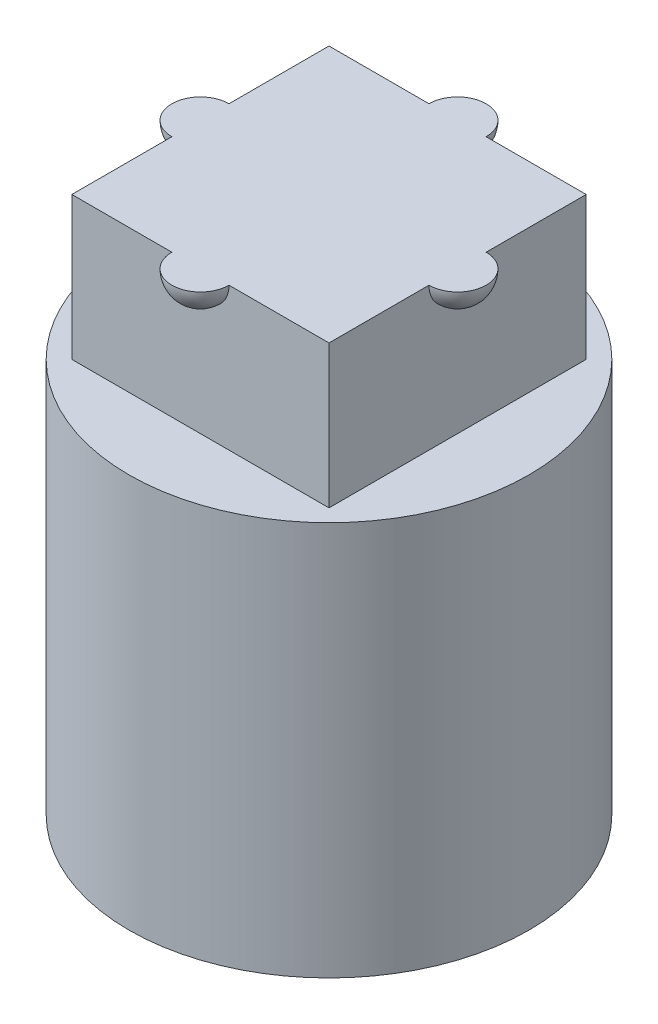
SolidWorks part; units mm, degrees
ref_plane "前视基准面" through (0, 0, 0) normal (0, 0, 1) x (1, 0, 0)
ref_plane "上视基准面" through (0, 0, 0) normal (0, 1, 0) x (1, 0, 0)
ref_plane "右视基准面" through (0, 0, 0) normal (1, 0, 0) x (0, 0, -1)
sketch "草图1" plane through (0, 0, 0) normal (0, 1, 0) x (1, 0, 0)
  line L0 (-1.85, 0) -> (1.85, 0) construction
  line L1 (-2.25, 2.25) -> (-0.4, 2.25)
  line L2 (-2.25, 2.25) -> (-2.25, 0.4)
  line L3 (-2.25, -2.25) -> (-0.4, -2.25)
  line L4 (2.25, 2.25) -> (2.25, 0.4)
  line L5 (-2.25, 2.25) -> (2.25, -2.25) construction
  line L6 (-2.25, -2.25) -> (2.25, 2.25) construction
  line L7 (0, 1.85) -> (0, -1.85) construction
  line L8 (0.4, 2.25) -> (2.25, 2.25)
  line L9 (-2.25, -0.4) -> (-2.25, -2.25)
  line L10 (0.4, -2.25) -> (2.25, -2.25)
  line L11 (2.25, -0.4) -> (2.25, -2.25)
  circle A0 centre (0, 0) radius 3.5
  arc A1 (0.4, 2.25) -> (-0.4, 2.25) centre (0, 2.25) ccw
  arc A2 (-2.25, 0.4) -> (-2.25, -0.4) centre (-2.25, 0) ccw
  arc A3 (-0.4, -2.25) -> (0.4, -2.25) centre (0, -2.25) ccw
  arc A4 (2.25, -0.4) -> (2.25, 0.4) centre (2.25, 0) ccw
  dimension "D1" = 7
  dimension "D4" = 0.8
  dimension "D5" = 0.8
  dimension "D6" = 0.8
  dimension "D7" = 0.8
  dimension "D2" = 4.5
  dimension "D3" = 4.5
extrude "凸台-拉伸1" add sketch "草图1" along normal blind 4
sketch "草图3" plane through (0, 4, 0) normal (0, 1, 0) x (1, 0, 0)
  circle A2 centre (0, 0) radius 3.5
  circle A3 centre (0, 0) radius 3.5
  dimension "D1" = 0
extrude "凸台-拉伸2" add sketch "草图3" along normal blind 2.9
sketch "草图4" plane through (0, 6.9, 0) normal (0, 1, 0) x (1, 0, 0)
  line L1 (-2.25, 2.25) -> (2.25, 2.25)
  line L2 (-2.25, 2.25) -> (-2.25, -2.25)
  line L3 (-2.25, -2.25) -> (2.25, -2.25)
  line L4 (2.25, 2.25) -> (2.25, -2.25)
  line L5 (-2.25, 2.25) -> (2.25, -2.25) construction
  line L6 (-2.25, -2.25) -> (2.25, 2.25) construction
  point P0 (0, 0)
  dimension "D1" = 4.5
  dimension "D2" = 4.5
extrude "凸台-拉伸3" add sketch "草图4" along normal blind 2.5
sketch "草图5" plane through (0, 9.4, 0) normal (0, 1, 0) x (1, 0, 0)
  line L0 (-2.25, 2.25) -> (-2.25, -2.25) construction
  line L1 (2.25, -2.25) -> (2.25, 2.25) construction
  line L2 (-2.75, 0) -> (-1.75, 0)
  line L3 (1.75, 0) -> (2.75, 0)
  arc A0 (-2.75, 0) -> (-1.75, 0) centre (-2.25, 0) ccw
  arc A1 (1.75, 0) -> (2.75, 0) centre (2.25, 0) ccw
  dimension "D1" = 1
  dimension "D2" = 1
revolve "旋转1" add sketch "草图5" angle 360 about L2
sketch "草图6" plane through (0, 9.4, 0) normal (0, 1, 0) x (1, 0, 0)
  line L0 (-2.25, -2.25) -> (2.25, -2.25) construction
  line L1 (2.25, 2.25) -> (-2.25, 2.25) construction
  line L2 (0, -2.75) -> (0, -1.75)
  line L3 (0, 1.75) -> (0, 2.75)
  arc A0 (0, -1.75) -> (0, -2.75) centre (0, -2.25) ccw
  arc A1 (0, 2.75) -> (0, 1.75) centre (0, 2.25) ccw
  dimension "D1" = 1
  dimension "D2" = 1
revolve "旋转2" add sketch "草图6" angle 360 about L2
sketch "草图7" plane through (0, 9.4, 0) normal (0, 1, 0) x (1, 0, 0)
  circle A0 centre (0, 0) radius 3.5
extrude "切除-拉伸1" cut sketch "草图7" along normal blind 10
